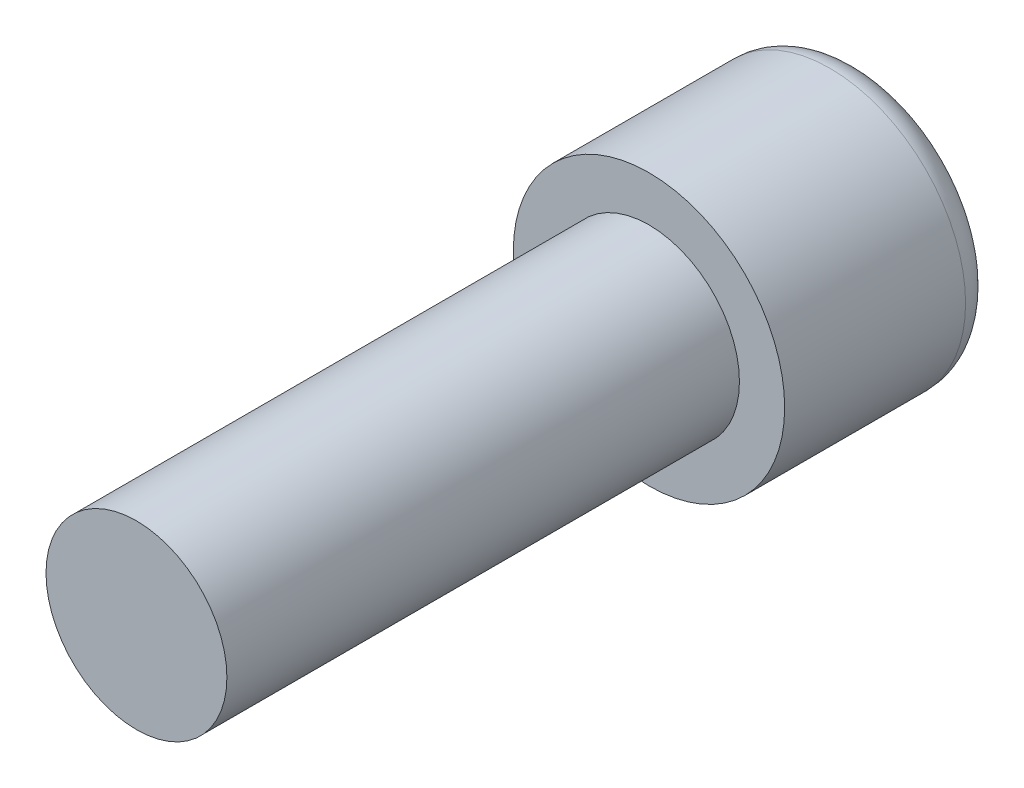
SolidWorks part; units mm, degrees
ref_plane "Front Plane" through (0, 0, 0) normal (0, 0, 1) x (1, 0, 0)
ref_plane "Top Plane" through (0, 0, 0) normal (0, 1, 0) x (1, 0, 0)
ref_plane "Right Plane" through (0, 0, 0) normal (1, 0, 0) x (0, 0, -1)
sketch "Sketch1" plane through (0, 0, 0) normal (0, 0, 1) x (1, 0, 0)
  circle A0 centre (0, 0) radius 0.75
  dimension "D1" = 1.5
extrude "Boss-Extrude1" add sketch "Sketch1" along normal blind 4.25
sketch "Sketch2" plane through (0, 0, 0) normal (0, 0, -1) x (-1, 0, 0)
  circle A0 centre (0, 0) radius 1.125
  dimension "D1" = 2.25
extrude "Boss-Extrude2" add sketch "Sketch2" along normal blind 1.75
fillet "Fillet1" radius 0.25 1 edges at (-1.125, 0, -1.75)
sketch "Sketch3" plane through (0, 0, -1.75) normal (0, 0, -1) x (-1, 0, 0)
  line L1 (0.2292, -0.6843) -> (0.7072, -0.1436)
  line L2 (0.7072, -0.1436) -> (0.478, 0.5407)
  line L3 (0.478, 0.5407) -> (-0.2292, 0.6843)
  line L4 (-0.2292, 0.6843) -> (-0.7072, 0.1436)
  line L5 (-0.7072, 0.1436) -> (-0.478, -0.5407)
  line L6 (-0.478, -0.5407) -> (0.2292, -0.6843)
  circle A0 centre (0, 0) radius 0.625 construction
  dimension "D1" = 1.25
extrude "Cut-Extrude1" cut sketch "Sketch3" against normal blind 1
